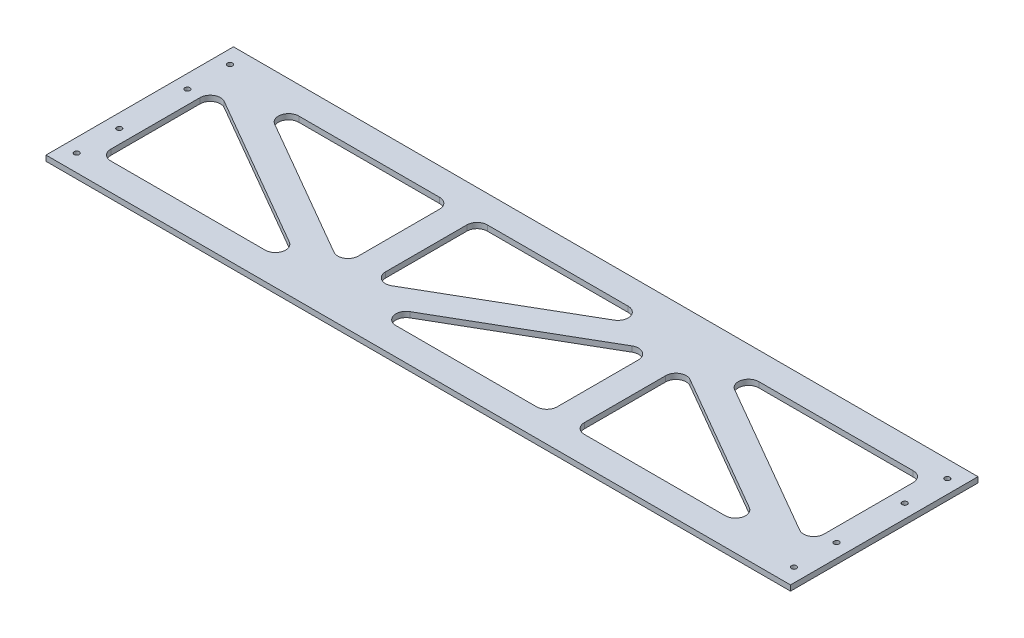
SolidWorks part; units mm, degrees
material "A-Glass Fiber"
ref_plane "Front Plane" through (0, 0, 0) normal (0, 0, 1) x (1, 0, 0)
ref_plane "Top Plane" through (0, 0, 0) normal (0, 1, 0) x (1, 0, 0)
ref_plane "Right Plane" through (0, 0, 0) normal (1, 0, 0) x (0, 0, -1)
sketch "Sketch1" plane through (0, 0, 0) normal (0, 1, 0) x (1, 0, 0)
  line L0 (0, 0) -> (0, 349.25)
  line L1 (0, 0) -> (1386.9289, 0)
  line L2 (0, 349.25) -> (1386.9289, 349.25)
  line L3 (1386.9289, 0) -> (1386.9289, 349.25)
  line L4 (50.8, 298.45) -> (1336.1289, 298.45)
  line L5 (1336.1289, 50.8) -> (1336.1289, 298.45)
  line L6 (50.8, 50.8) -> (1336.1289, 50.8)
  line L7 (50.8, 50.8) -> (50.8, 298.45)
  line L8 (479.243, 298.45) -> (479.243, 50.8)
  line L9 (907.6859, 298.45) -> (907.6859, 50.8)
  line L10 (50.8, 174.625) -> (479.243, 174.625) construction
  line L11 (479.243, 174.625) -> (907.6859, 174.625) construction
  line L12 (907.6859, 174.625) -> (1336.1289, 174.625) construction
  line L13 (50.8, 298.45) -> (453.843, 65.4818)
  line L14 (504.643, 65.4818) -> (882.2859, 283.7682)
  line L15 (933.0859, 283.7682) -> (1336.1289, 50.8)
  line L16 (50.8, 269.1121) -> (428.4873, 50.8)
  line L17 (529.9986, 50.8) -> (882.2859, 254.4303)
  line L18 (933.0859, 254.4303) -> (1285.3733, 50.8)
  line L19 (101.5556, 298.45) -> (453.843, 94.8197)
  line L20 (504.643, 94.8197) -> (856.9303, 298.45)
  line L21 (958.4416, 298.45) -> (1336.1289, 80.1379)
  line L22 (882.2859, 298.45) -> (882.2859, 50.8)
  line L23 (38.0889, 276.4594) -> (466.5319, 28.8094) construction
  line L24 (63.5111, 320.4406) -> (491.9541, 72.7906) construction
  line L25 (466.5319, 72.7906) -> (894.9748, 320.4406) construction
  line L26 (491.9541, 28.8094) -> (920.397, 276.4594) construction
  line L27 (920.397, 320.4406) -> (1348.84, 72.7906) construction
  line L28 (894.9748, 276.4594) -> (1323.4178, 28.8094) construction
  line L29 (933.0859, 298.45) -> (933.0859, 50.8)
  line L30 (453.843, 298.45) -> (453.843, 50.8)
  line L31 (504.643, 298.45) -> (504.643, 50.8)
  line L33 (479.243, 50.8) -> (907.6859, 298.45) construction
  line L34 (50.8, 298.45) -> (479.243, 50.8) construction
  line L35 (907.6859, 298.45) -> (1336.1289, 50.8) construction
  dimension "D1" = 349.25
  dimension "D2" = 1386.9289
  dimension "D4" = 25.4
  dimension "D3" = 50.8
  dimension "D5" = 25.4
  dimension "D6" = 25.4
  dimension "D7" = 25.4
  dimension "D8" = 25.4
  dimension "D9" = 25.4
extrude "Boss-Extrude1" add sketch "Sketch1" along normal blind 10.16 contours L1 L3 L2 L0 L6 L7 L4 L5 | L30 L13 L7 L16 L6 | L30 L19 L4 L13 | L4 L30 L6 L8 | L31 L4 L8 L6 | L20 L31 L14 L22 L4 | L14 L31 L6 L17 L22 | L4 L22 L6 L9 | L29 L4 L9 L6 | L15 L29 L18 L6 | L4 L29 L15 L5 L21
fillet "Fillet1" radius 19.05 18 edges at (1336.1289, 5.08, -298.45) (1336.1289, 5.08, -80.1379) (958.4416, 5.08, -298.45) (933.0859, 5.08, -254.4303) (933.0859, 5.08, -50.8) (1285.3733, 5.08, -50.8) (882.2859, 5.08, -50.8) (529.9986, 5.08, -50.8) (882.2859, 5.08, -254.4303) (856.9303, 5.08, -298.45) (504.643, 5.08, -94.8197) (504.643, 5.08, -298.45) (50.8, 5.08, -50.8) (50.8, 5.08, -269.1121) (101.5556, 5.08, -298.45) (428.4873, 5.08, -50.8) (453.843, 5.08, -94.8197) (453.843, 5.08, -298.45)
sketch "Sketch2" plane through (0, 0, 0) normal (-1, 0, 0) x (0, 0, 1)
  line L0 (-371.475, 11.7475) -> (-371.475, 10.16)
  line L1 (0, 10.16) -> (-349.25, 10.16) construction
  line L2 (-9.525, 16.51) -> (-9.525, 10.16)
  line L3 (3.175, 16.51) -> (3.175, 10.16)
  line L4 (-9.525, 10.16) -> (-28.575, 10.16)
  line L5 (3.175, 10.16) -> (22.225, 10.16)
  line L6 (-174.625, 10.16) -> (-174.625, 0) construction
  line L7 (0, 0) -> (-349.25, 0) construction
  line L8 (-352.425, 10.16) -> (-371.475, 10.16)
  line L9 (-339.725, 10.16) -> (-320.675, 10.16)
  line L10 (-352.425, 16.51) -> (-352.425, 10.16)
  line L11 (-339.725, 16.51) -> (-339.725, 10.16)
  line L12 (-354.0125, 16.51) -> (-354.0125, 11.7475)
  line L13 (-354.0125, 11.7475) -> (-371.475, 11.7475)
  line L14 (-338.1375, 16.51) -> (-338.1375, 11.7475)
  line L15 (-338.1375, 11.7475) -> (-320.675, 11.7475)
  line L16 (-320.675, 11.7475) -> (-320.675, 10.16)
  line L17 (-28.575, 11.7475) -> (-28.575, 10.16)
  line L18 (-11.1125, 11.7475) -> (-28.575, 11.7475)
  line L19 (-11.1125, 16.51) -> (-11.1125, 11.7475)
  line L20 (4.7625, 16.51) -> (4.7625, 11.7475)
  line L21 (4.7625, 11.7475) -> (22.225, 11.7475)
  line L22 (22.225, 11.7475) -> (22.225, 10.16)
  circle A0 centre (-3.175, 16.51) radius 6.35
  circle A1 centre (-346.075, 16.51) radius 6.35
  arc A2 (-338.1375, 16.51) -> (-354.0125, 16.51) centre (-346.075, 16.51) ccw
  arc A3 (-11.1125, 16.51) -> (4.7625, 16.51) centre (-3.175, 16.51) cw
  dimension "D1" = 12.7
  dimension "D2" = 19.05
  dimension "D3" = 19.05
  dimension "D4" = 342.9
  dimension "D5" = 1.5875
  dimension "D6" = 1.5875
sketch "Sketch4" plane through (0, 10.16, 0) normal (0, 1, 0) x (1, 0, 0)
  line L0 (0, 0) -> (0, 349.25) construction
  line L1 (0, 349.25) -> (1386.9289, 349.25) construction
  line L2 (25.4, 317.5) -> (25.4, 31.75) construction
  line L3 (1386.9289, 0) -> (1386.9289, 349.25) construction
  line L4 (1361.5289, 317.5) -> (1361.5289, 31.75) construction
  circle A0 centre (25.4, 317.5) radius 4.7625
  circle A1 centre (25.4, 238.125) radius 4.7625
  circle A3 centre (25.4, 111.125) radius 4.7625
  circle A4 centre (25.4, 31.75) radius 4.7625
  circle A5 centre (1361.5289, 31.75) radius 4.7625
  circle A6 centre (1361.5289, 111.125) radius 4.7625
  circle A7 centre (1361.5289, 238.125) radius 4.7625
  circle A8 centre (1361.5289, 317.5) radius 4.7625
  dimension "D1" = 9.525
  dimension "D2" = 25.4
  dimension "D3" = 31.75
  dimension "D4" = 79.375
  dimension "D5" = 31.75
  dimension "D6" = 25.4
  dimension "D7" = 79.375
extrude "Cut-Extrude1" cut sketch "Sketch4" against normal through all
